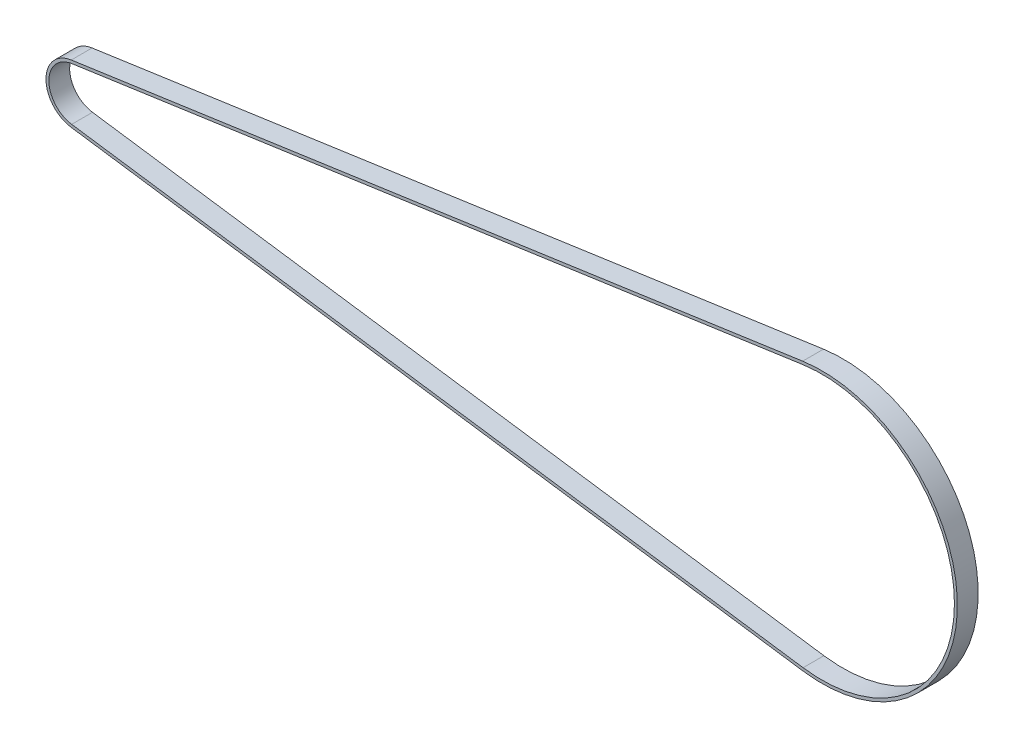
SolidWorks part; units mm, degrees
ref_plane "Front Plane" through (0, 0, 0) normal (0, 0, 1) x (1, 0, 0)
ref_plane "Top Plane" through (0, 0, 0) normal (0, 1, 0) x (1, 0, 0)
ref_plane "Right Plane" through (0, 0, 0) normal (1, 0, 0) x (0, 0, -1)
sketch "Sketch2" plane through (0, 0, 0) normal (0, 0, 1) x (1, 0, 0)
  line L0 (0, 0) -> (1, 0) construction
  line L1 (0, 0) -> (0, 1) construction
  line L2 (-2.5778, 17.9771) -> (497.1471, 89.6342)
  line L3 (497.1471, -89.6342) -> (-2.5778, -17.9771)
  arc A0 (-2.5778, -17.9771) -> (-2.5778, 17.9771) centre (0, 0) cw
  arc A1 (497.1471, 89.6342) -> (497.1471, -89.6342) centre (510, 0) cw
extrude "Extrude-Thin1" add sketch "Sketch2" along normal blind 14.224 thin thin type one direction wall 2
